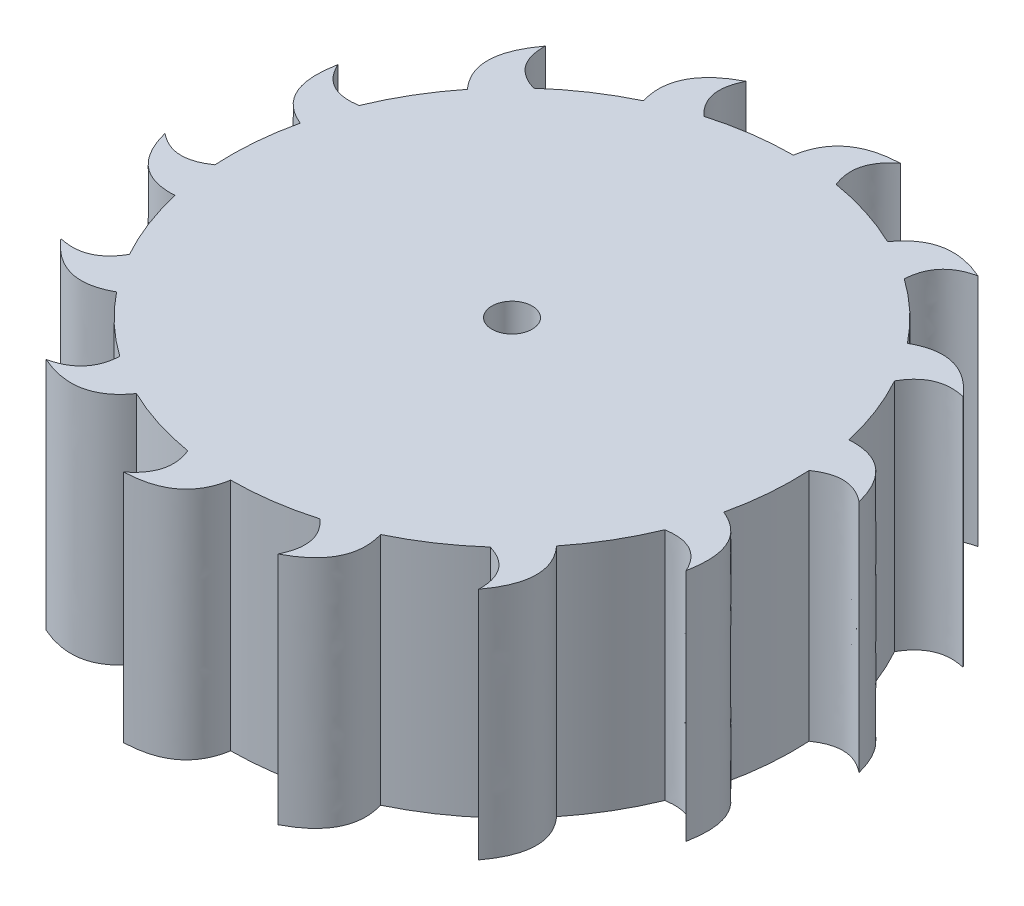
SolidWorks part; units mm, degrees
ref_plane "Front Plane" through (0, 0, 0) normal (0, 0, 1) x (1, 0, 0)
ref_plane "Top Plane" through (0, 0, 0) normal (0, 1, 0) x (1, 0, 0)
ref_plane "Right Plane" through (0, 0, 0) normal (1, 0, 0) x (0, 0, -1)
sketch "Sketch1" plane through (0, 0, 0) normal (0, 1, 0) x (1, 0, 0)
  circle A0 centre (0, 0) radius 30
  dimension "D1" = 60
extrude "Boss-Extrude1" add sketch "Sketch1" along normal blind 25
sketch "Sketch2" plane through (0, 25, 0) normal (0, 1, 0) x (1, 0, 0)
  circle A0 centre (0, 0) radius 2.15
  dimension "D1" = 4.3
extrude "Cut-Extrude1" cut sketch "Sketch2" against normal through all contours A0
ref_plane "Plane1" through (0, 25, 0) normal (0, 1, 0) x (1, 0, 0)
sketch "Sketch3" plane through (0, 25, 0) normal (0, 1, 0) x (1, 0, 0)
  line L13 (0, 30) -> (3.379, 26.8099)
  line L14 (3.379, 26.8099) -> (4.9777, 29.5842)
  circle A4 centre (0, 0) radius 30 construction
  spline S0 degree 2 poles (0, 30) (0.7745, 34.7746) (6.4631, 34.9585) knots 0 0 0 1 1 1
  spline S1 degree 2 poles (6.4631, 34.9585) (3.6781, 32.8105) (4.9777, 29.5842) knots 0 0 0 1 1 1
extrude "Boss-Extrude2" add sketch "Sketch3" against normal through all
pattern_circular "CirPattern1" count 14 over 360 about axis through (0, 0, 0) along (0, 1, 0) of "Boss-Extrude2"
